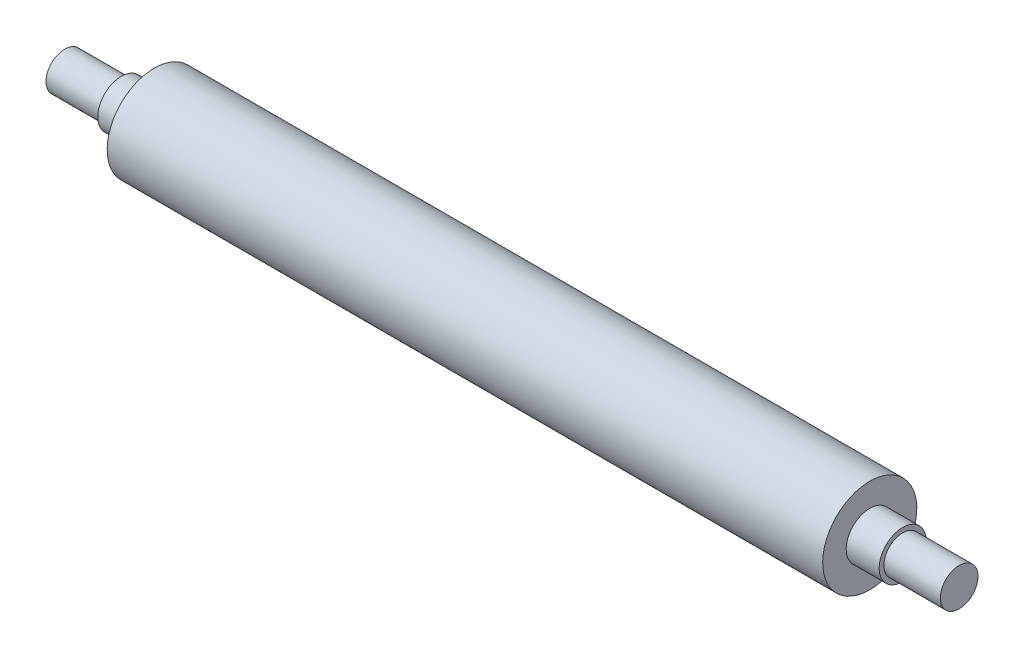
SolidWorks part; units mm, degrees
ref_plane "前视基准面" through (0, 0, 0) normal (0, 0, 1) x (1, 0, 0)
ref_plane "上视基准面" through (0, 0, 0) normal (0, 1, 0) x (1, 0, 0)
ref_plane "右视基准面" through (0, 0, 0) normal (1, 0, 0) x (0, 0, -1)
sketch "草图1" plane through (0, 0, 0) normal (0, 0, 1) x (1, 0, 0)
  line L0 (-230.7094, 0) -> (459.7941, 0) construction
  line L1 (0, 215.5466) -> (0, -189.8195) construction
  line L2 (-190, 25) -> (190, 25)
  line L6 (-237.5, 10) -> (-237.5, 0)
  line L7 (-207.5, 10) -> (-237.5, 10)
  line L8 (-190, 25) -> (-190, 12.5)
  line L9 (-237.5, 0) -> (237.5, 0)
  line L10 (-207.5, 10) -> (-207.5, 12.5)
  line L11 (-207.5, 12.5) -> (-190, 12.5)
  line L12 (237.5, 10) -> (237.5, 0)
  line L13 (207.5, 10) -> (237.5, 10)
  line L14 (207.5, 10) -> (207.5, 12.5)
  line L15 (207.5, 12.5) -> (190, 12.5)
  line L16 (190, 25) -> (190, 12.5)
  point P17 (0, 25)
  dimension "D1" = 12.5
  dimension "D2" = 10
  dimension "D3" = 25
  dimension "D4" = 380
  dimension "D5" = 30
  dimension "D6" = 415
revolve "旋转1" add sketch "草图1" angle 360 about L9
